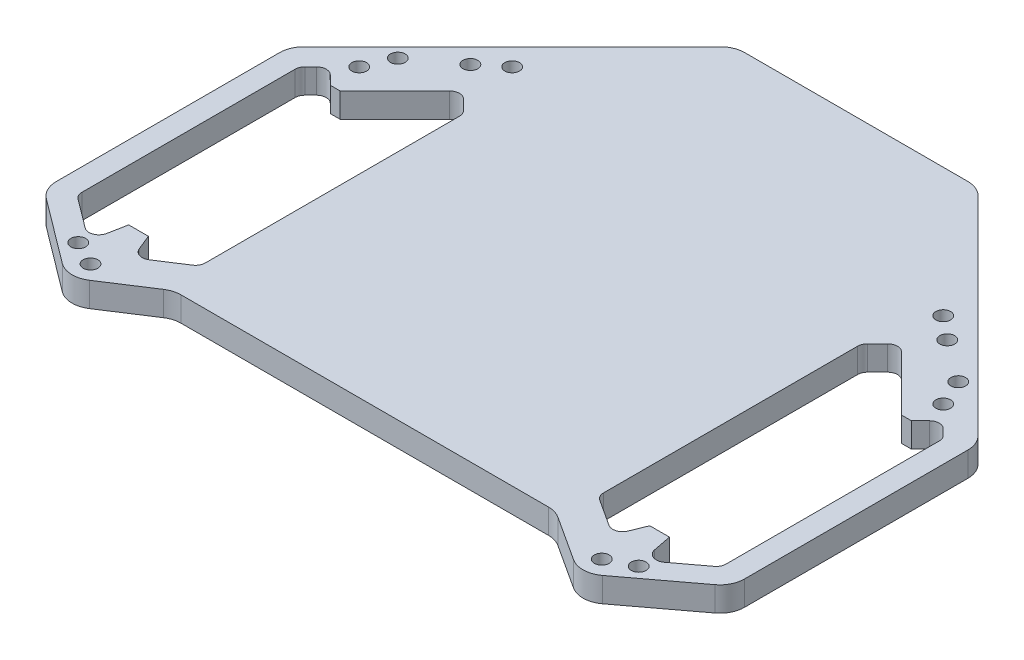
SolidWorks part; units mm, degrees
ref_plane "Front Plane" through (0, 0, 0) normal (0, 0, 1) x (1, 0, 0)
ref_plane "Top Plane" through (0, 0, 0) normal (0, 1, 0) x (1, 0, 0)
ref_plane "Right Plane" through (0, 0, 0) normal (1, 0, 0) x (0, 0, -1)
sketch "Sketch1" plane through (0, 0, 0) normal (0, 1, 0) x (1, 0, 0)
  line L0 (-52.1641, -38.6452) -> (-70, -25.2479)
  line L1 (-70, -25.2479) -> (-70, 24.7523)
  line L2 (-70, 24.7523) -> (-24.7523, 70)
  line L3 (-52.1641, -38.6452) -> (-38.8516, -30)
  line L4 (0, -30) -> (0, 70)
  line L5 (0, -30) -> (-38.8516, -30)
  line L6 (-59.397, 28.2843) -> (-43.8406, 43.8406) construction
  line L7 (-51.9976, -33.7676) -> (-63.9796, -15.3169) construction
  line L8 (-24.7523, 70) -> (0, 70)
  line L9 (0, 0) -> (-85, 0) construction
  line L10 (-43.8406, 43.8406) -> (0, 0) construction
  line L11 (-51.9976, -33.7676) -> (0, 0) construction
  line L12 (-59.096, 22.1) -> (-57.096, 22.1)
  line L13 (-65.5, 22.1812) -> (-65.5, -23)
  line L14 (-55, -23) -> (-51, -23)
  line L15 (-40.5, 30.6005) -> (-40.5, -23)
  line L16 (-53, 22.1) -> (-53, -23) construction
  line L17 (-65.5, 22.1812) -> (-62.3386, 25.3426)
  line L18 (-62.3386, 25.3426) -> (-59.096, 22.1)
  line L19 (-57.096, 22.1) -> (-44.5477, 34.6482)
  line L20 (-44.5477, 34.6482) -> (-40.5, 30.6005)
  line L21 (-65.5, -23) -> (-56.3366, -29.883)
  line L22 (-56.3366, -29.883) -> (-55, -23)
  line L23 (-51, -23) -> (-48.7962, -28.3876)
  line L24 (-48.7962, -28.3876) -> (-40.5, -23)
  line L25 (-50, 65) -> (-20, 80) construction
  line L26 (-20, 80) -> (0, 80) construction
  line L27 (0, 80) -> (0, 4) construction
  line L28 (0, 4) -> (-50, 4) construction
  line L29 (-50, 65) -> (-50, 4) construction
  circle A0 centre (0, 0) radius 85 construction
  circle A1 centre (-43.8406, 43.8406) radius 1.5
  circle A2 centre (-51.9976, -33.7676) radius 1.5
  circle A3 centre (-59.397, 28.2843) radius 1.5
  circle A4 centre (-63.9796, -15.3169) radius 1.5 construction
  circle A5 centre (-56.9976, 33.7374) radius 1.5
  circle A6 centre (-56.9976, -31.2626) radius 1.5
  circle A7 centre (-48.5, 40) radius 1.5
  dimension "D7" = 3
  dimension "D17" = 170
  dimension "D20" = 12.5
  dimension "D2" = 30
  dimension "D3" = 4
  dimension "D4" = 4
  dimension "D5" = 4.5
  dimension "D6" = 70
  dimension "D8" = 62
  dimension "D9" = 22
  dimension "D10" = 22
  dimension "D11" = 25
  dimension "D12" = 45.1
  dimension "D13" = 53
  dimension "D14" = 45
  dimension "D15" = 33
  dimension "D16" = 23
  dimension "D18" = 5
  dimension "D19" = 70
  dimension "D21" = 5
  dimension "D22" = 5
  dimension "D23" = 4
  dimension "D24" = 6
  dimension "D25" = 15
  dimension "D26" = 65
  dimension "D27" = 5
  dimension "D28" = 3
  dimension "D29" = 50
  dimension "D30" = 30
  dimension "D31" = 15
  dimension "D32" = 80
  dimension "D33" = 76
  dimension "D34" = 2
  dimension "D35" = 40
extrude "Boss-Extrude1" add sketch "Sketch1" along normal blind 5
fillet "Fillet1" radius 2 8 edges at (-40.5, 2.5, 23) (-48.7962, 2.5, 28.3876) (-56.3366, 2.5, 29.883) (-65.5, 2.5, 23) (-65.5, 2.5, -22.1812) (-62.3386, 2.5, -25.3426) (-40.5, 2.5, -30.6005) (-44.5477, 2.5, -34.6482)
mirror "Mirror1" about plane through (0, 5, 30) normal (-1, 0, 0) of "Fillet1", "Boss-Extrude1"
sketch "Sketch2" plane through (0, 0, 0) normal (0, 1, 0) x (1, 0, 0)
  line L0 (24.7523, 70) -> (-24.7523, 70) construction
  line L1 (-35, 70) -> (35, 70)
  line L2 (-35, 70) -> (-35, -27)
  line L3 (-35, -27) -> (35, -27)
  line L4 (35, 70) -> (35, -27)
  line L5 (-38.8516, -30) -> (38.8516, -30) construction
  dimension "D1" = 3
  dimension "D2" = 70
  dimension "D3" = 35
extrude "Cut-Extrude1" cut sketch "Sketch2" along normal blind 3
fillet "Fillet2" radius 5 10 edges at (-70, 2.5, 25.2479) (-70, 2.5, -24.7523) (-24.7523, 4, -70) (24.7523, 4, -70) (70, 2.5, -24.7523) (70, 2.5, 25.2479) (52.1641, 2.5, 38.6452) (38.8516, 2.5, 30) (-38.8516, 2.5, 30) (-52.1641, 2.5, 38.6452)
